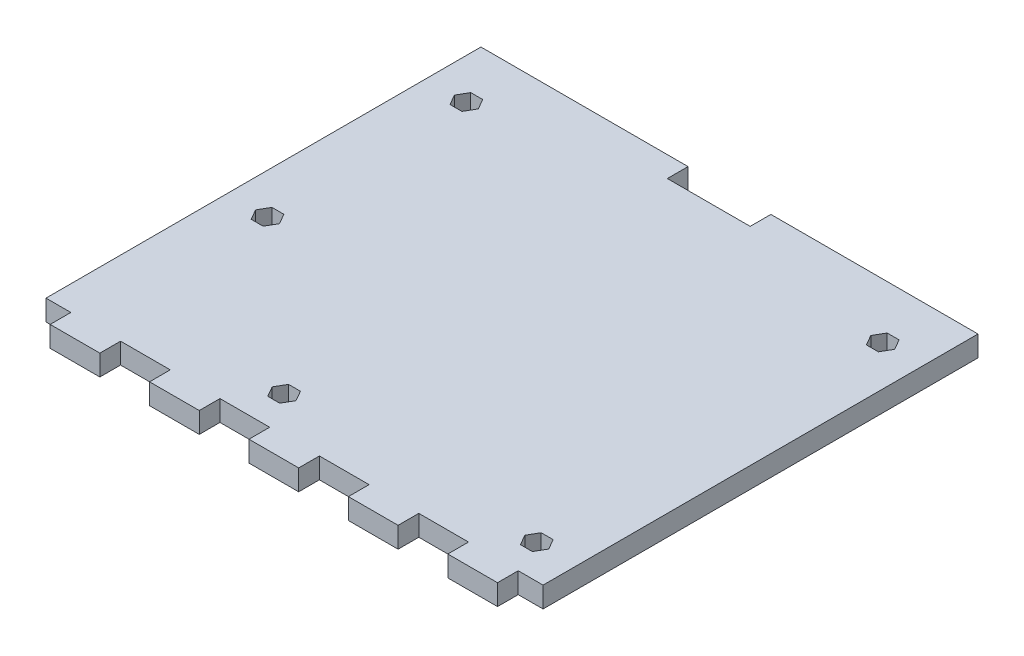
SolidWorks part; units mm, degrees
ref_plane "Front Plane" through (0, 0, 0) normal (0, 0, 1) x (1, 0, 0)
ref_plane "Top Plane" through (0, 0, 0) normal (0, 1, 0) x (1, 0, 0)
ref_plane "Right Plane" through (0, 0, 0) normal (1, 0, 0) x (0, 0, -1)
sketch "Sketch1" plane through (0, 0, 0) normal (0, 1, 0) x (1, 0, 0)
  line L0 (-19.05, -34.925) -> (-19.05, -31.75)
  line L1 (-34.29, -34.925) -> (-26.67, -34.925)
  line L2 (-38.1, -31.75) -> (-38.1, 34.925)
  line L3 (-38.1, 34.925) -> (-6.35, 34.925)
  line L4 (38.1, -31.75) -> (38.1, 34.925)
  line L5 (-34.6364, -31.75) -> (38.1, 34.925) construction
  line L6 (-38.1, 34.925) -> (34.6364, -31.75) construction
  line L8 (-34.29, -34.925) -> (-34.29, -31.75)
  line L9 (-34.29, -31.75) -> (-38.1, -31.75)
  line L12 (-26.67, -34.925) -> (-26.67, -31.75)
  line L13 (-19.05, -31.75) -> (-26.67, -31.75)
  line L14 (-3.81, -34.925) -> (-3.81, -31.75)
  line L16 (-11.43, -34.925) -> (-11.43, -31.75)
  line L17 (-3.81, -31.75) -> (-11.43, -31.75)
  line L18 (11.43, -34.925) -> (11.43, -31.75)
  line L20 (3.81, -34.925) -> (3.81, -31.75)
  line L21 (11.43, -31.75) -> (3.81, -31.75)
  line L22 (26.67, -34.925) -> (26.67, -31.75)
  line L24 (19.05, -34.925) -> (19.05, -31.75)
  line L25 (26.67, -31.75) -> (19.05, -31.75)
  line L28 (34.29, -34.925) -> (34.29, -31.75)
  line L29 (38.1, -31.75) -> (34.29, -31.75)
  line L30 (-19.05, -34.925) -> (-11.43, -34.925)
  line L31 (-30.9986, -5.5626) -> (-30.082, -3.9751)
  line L32 (-30.082, -3.9751) -> (-30.9986, -2.3876)
  line L33 (-30.9986, -2.3876) -> (-32.8316, -2.3876)
  line L34 (-32.8316, -2.3876) -> (-33.7482, -3.9751)
  line L35 (-33.7482, -3.9751) -> (-32.8316, -5.5626)
  line L36 (-32.8316, -5.5626) -> (-30.9986, -5.5626)
  line L37 (-30.082, 26.5049) -> (-30.9986, 28.0924)
  line L38 (-30.9986, 28.0924) -> (-32.8316, 28.0924)
  line L39 (-32.8316, 28.0924) -> (-33.7482, 26.5049)
  line L40 (-33.7482, 26.5049) -> (-32.8316, 24.9174)
  line L41 (-32.8316, 24.9174) -> (-30.9986, 24.9174)
  line L42 (-30.9986, 24.9174) -> (-30.082, 26.5049)
  line L43 (32.8316, 24.9174) -> (33.7482, 26.5049)
  line L44 (33.7482, 26.5049) -> (32.8316, 28.0924)
  line L45 (32.8316, 28.0924) -> (30.9986, 28.0924)
  line L46 (30.9986, 28.0924) -> (30.082, 26.5049)
  line L47 (30.082, 26.5049) -> (30.9986, 24.9174)
  line L48 (30.9986, 24.9174) -> (32.8316, 24.9174)
  line L49 (-6.2336, -27.7876) -> (-5.317, -26.2001)
  line L50 (-5.317, -26.2001) -> (-6.2336, -24.6126)
  line L51 (-6.2336, -24.6126) -> (-8.0666, -24.6126)
  line L52 (-8.0666, -24.6126) -> (-8.9832, -26.2001)
  line L53 (-8.9832, -26.2001) -> (-8.0666, -27.7876)
  line L54 (-8.0666, -27.7876) -> (-6.2336, -27.7876)
  line L55 (33.7482, -26.5303) -> (32.8316, -24.9428)
  line L56 (32.8316, -24.9428) -> (30.9986, -24.9428)
  line L57 (30.9986, -24.9428) -> (30.082, -26.5303)
  line L58 (30.082, -26.5303) -> (30.9986, -28.1178)
  line L59 (30.9986, -28.1178) -> (32.8316, -28.1178)
  line L60 (32.8316, -28.1178) -> (33.7482, -26.5303)
  line L62 (-6.35, 34.925) -> (-6.35, 31.75)
  line L63 (-6.35, 31.75) -> (6.35, 31.75)
  line L64 (6.35, 34.925) -> (6.35, 31.75)
  line L65 (-3.81, -34.925) -> (3.81, -34.925)
  line L66 (11.43, -34.925) -> (19.05, -34.925)
  line L67 (26.67, -34.925) -> (34.29, -34.925)
  line L68 (41.91, -34.925) -> (41.91, -31.75) [skipped]
  line L69 (6.35, 34.925) -> (38.1, 34.925)
  circle A0 centre (-31.9151, -3.9751) radius 1.5875 construction
  circle A1 centre (-31.9151, 26.5049) radius 1.5875 construction
  circle A2 centre (31.9151, 26.5049) radius 1.5875 construction
  circle A3 centre (-7.1501, -26.2001) radius 1.5875 construction
  circle A4 centre (31.9151, -26.5303) radius 1.5875 construction
  point P0 (0, 0)
  point P31 (-34.1249, -28.7401)
  dimension "D7" = 3.175
  dimension "D12" = 3.175
  dimension "D13" = 3.175
  dimension "D14" = 3.175
  dimension "D15" = 3.175
  dimension "D2" = 76.2
  dimension "D8" = 3.9751
  dimension "D9" = 6.1849
  dimension "D10" = 2.2098
  dimension "D11" = 24.765
  dimension "D16" = 2.2098
  dimension "D17" = 55.245
  dimension "D18" = 55.245
  dimension "D19" = 66.04
  dimension "D20" = 2.2098
  dimension "D21" = 66.04
  dimension "D22" = 2.54
  dimension "D23" = 26.9748
  dimension "D24" = 3.175
  dimension "D25" = 12.7
  dimension "D6" = 6
extrude "Boss-Extrude2" add sketch "Sketch1" along normal blind 3.175
